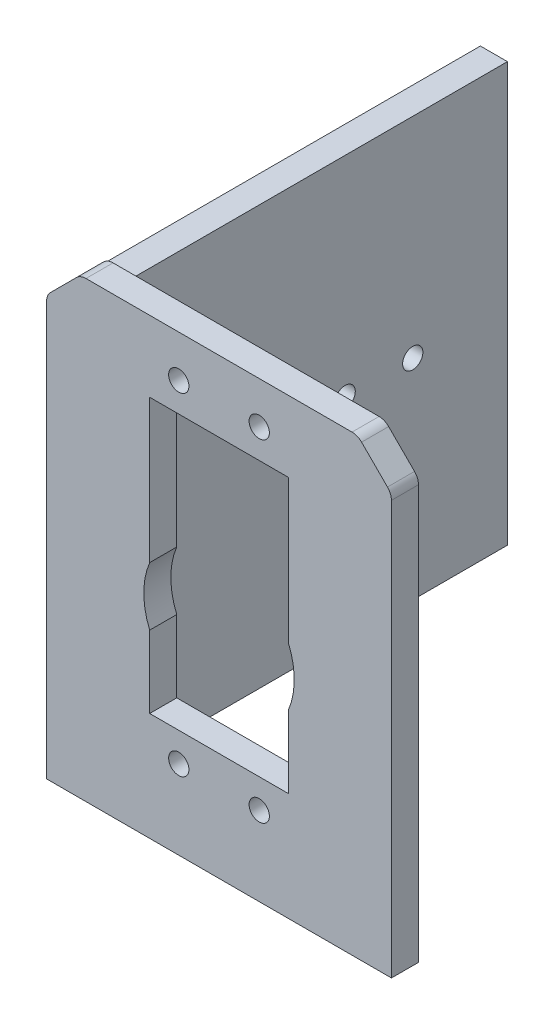
SolidWorks part; units mm, degrees
ref_plane "Front Plane" through (0, 0, 0) normal (0, 0, 1) x (1, 0, 0)
ref_plane "Top Plane" through (0, 0, 0) normal (0, 1, 0) x (1, 0, 0)
ref_plane "Right Plane" through (0, 0, 0) normal (1, 0, 0) x (0, 0, -1)
sketch "Sketch1" plane through (0, 0, 0) normal (0, 0, 1) x (1, 0, 0)
  line L12 (0, 61.1716) -> (0, 0)
  line L13 (0, 0) -> (51, 0)
  line L14 (51, 0) -> (51, 61.1716)
  line L15 (50.4142, 62.5858) -> (46.5858, 66.4142)
  line L16 (45.1716, 67) -> (5.8284, 67)
  line L17 (4.4142, 66.4142) -> (0.5858, 62.5858)
  line L18 (15.25, 56.5) -> (35.75, 56.5)
  line L19 (15.25, 16) -> (15.25, 26.6753)
  line L20 (15.25, 35.3247) -> (15.25, 56.5)
  line L21 (35.75, 56.5) -> (35.75, 35.3247)
  line L22 (35.75, 26.6753) -> (35.75, 16)
  line L23 (35.75, 16) -> (15.25, 16)
  arc A8 (51, 61.1716) -> (50.4142, 62.5858) centre (49, 61.1716) ccw
  arc A9 (46.5858, 66.4142) -> (45.1716, 67) centre (45.1716, 65) ccw
  arc A10 (5.8284, 67) -> (4.4142, 66.4142) centre (5.8284, 65) ccw
  arc A11 (0.5858, 62.5858) -> (0, 61.1716) centre (2, 61.1716) ccw
  arc A14 (15.25, 35.3247) -> (15.25, 26.6753) centre (25.5, 31) ccw
  arc A15 (35.75, 26.6753) -> (35.75, 35.3247) centre (25.5, 31) ccw
  circle A16 centre (19.55, 11.7) radius 1.5
  circle A17 centre (31.45, 11.7) radius 1.5
  circle A18 centre (31.45, 60.8) radius 1.5
  circle A19 centre (19.55, 60.8) radius 1.5
extrude "Boss-Extrude3" add sketch "Sketch1" along normal blind 4
sketch "Sketch2" plane through (0, 0, 0) normal (0, 0, -1) x (-1, 0, 0)
  line L0 (0, 0) -> (-51, 0) construction
  line L1 (-0.1522, 61.9369) -> (-4.1522, 61.9369)
  line L2 (-0.1522, 61.9369) -> (-0.1522, 0)
  line L3 (-0.1522, 0) -> (-4.1522, 0)
  line L4 (-4.1522, 61.9369) -> (-4.1522, 0)
  arc A0 (0, 61.1716) -> (-0.5858, 62.5858) centre (-2, 61.1716) ccw construction
extrude "Boss-Extrude4" add sketch "Sketch2" along normal blind 60
sketch "Sketch3" plane through (0.1522, 0, 0) normal (-1, 0, 0) x (0, 0, 1)
  line L0 (-60, 30.9685) -> (0, 30.9685) construction
  line L1 (-60, 0) -> (-60, 61.9369) construction
  line L2 (0, 0) -> (0, 61.9369) construction
  circle A0 centre (-46, 30.9685) radius 1.5
  circle A1 centre (-36, 30.9685) radius 1.5
  point P10 (0, 0)
  point P11 (0, 0)
  point P12 (0, 0)
  point P13 (0, 0)
  point P14 (0, 0)
  point P15 (0, 0)
  point P16 (0, 0)
  point P17 (0, 0)
  point P18 (0, 0)
  point P19 (0, 0)
  point P20 (0, 0)
  point P21 (0, 0)
  point P22 (0, 0)
  point P23 (0, 0)
  point P24 (0, 0)
extrude "Cut-Extrude2" cut sketch "Sketch3" against normal blind 10
